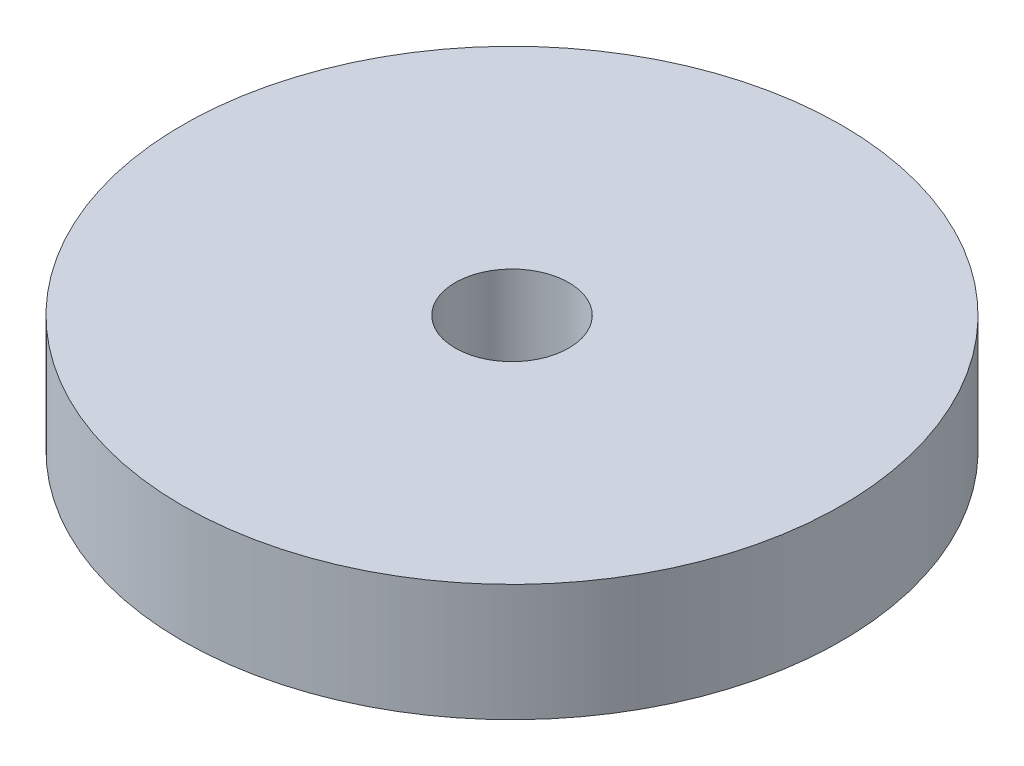
SolidWorks part; units mm, degrees
ref_plane "Front Plane" through (0, 0, 0) normal (0, 0, 1) x (1, 0, 0)
ref_plane "Top Plane" through (0, 0, 0) normal (0, 1, 0) x (1, 0, 0)
ref_plane "Right Plane" through (0, 0, 0) normal (1, 0, 0) x (0, 0, -1)
sketch "Sketch1" plane through (0, 0, 0) normal (0, 1, 0) x (1, 0, 0)
  circle A0 centre (0, 0) radius 250
  circle A1 centre (0, 0) radius 43.075
  dimension "D1" = 500
  dimension "D2" = 86.15
extrude "Boss-Extrude1" add sketch "Sketch1" along normal blind 88.9
